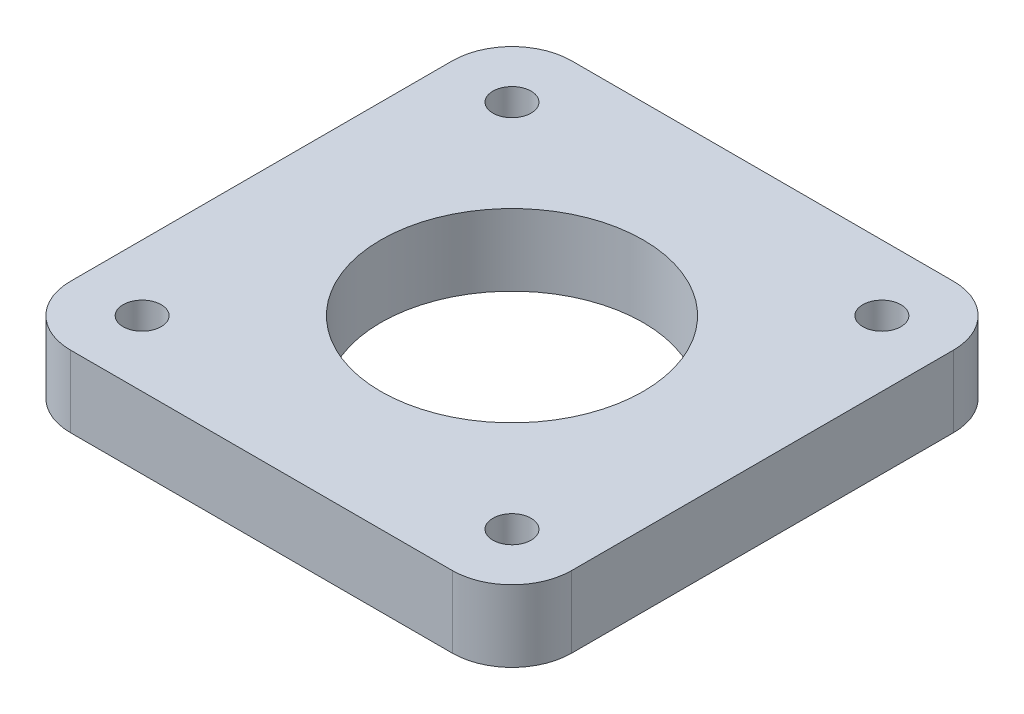
SolidWorks part; units mm, degrees
material "Maple"
ref_plane "Front Plane" through (0, 0, 0) normal (0, 0, 1) x (1, 0, 0)
ref_plane "Top Plane" through (0, 0, 0) normal (0, 1, 0) x (1, 0, 0)
ref_plane "Right Plane" through (0, 0, 0) normal (1, 0, 0) x (0, 0, -1)
sketch "Sketch1" plane through (0, 0, 0) normal (0, 1, 0) x (1, 0, 0)
  line L1 (-21, 21) -> (21, 21)
  line L2 (-21, 21) -> (-21, -21)
  line L3 (-21, -21) -> (21, -21)
  line L4 (21, 21) -> (21, -21)
  line L5 (-21, 21) -> (21, -21) construction
  line L6 (-21, -21) -> (21, 21) construction
  point P0 (0, 0)
  dimension "D1" = 42
extrude "Boss-Extrude1" add sketch "Sketch1" along normal blind 6
ref_plane "Plane1" through (0, 3, 0) normal (0, 1, 0) x (1, 0, 0)
hole_wizard "M3 Clearance Hole1" positions "Sketch5" profile "Sketch4" hole size "M3" standard "ANSI Metric" end condition through all
sketch "Sketch5" plane through (0, 0, 0) normal (0, -1, 0) x (0, 0, -1)
  circle A0 centre (-15.5, -15.5) radius 1.5 construction
  circle A1 centre (-15.5, 15.5) radius 1.5 construction
  circle A2 centre (15.5, 15.5) radius 1.5 construction
  circle A3 centre (15.5, -15.5) radius 1.5 construction
  point P0 (15.5, -15.5)
  point P2 (-15.5, -15.5)
  point P4 (-15.5, 15.5)
  point P6 (15.5, 15.5)
sketch "Sketch4" plane through (-15.5, 0, -15.5) normal (1, 0, 0) x (0, 0, -1)
  line L0 (0, 0) -> (0, 6)
  line L1 (0, 6) -> (1.6, 6)
  line L2 (1.6, 6) -> (1.6, 0)
  line L5 (1.6, 0) -> (0, 0)
  line L11 (0, -6.35) -> (0, 107.95) construction
  dimension "Thru Hole Dia." = 3.2
  dimension "Thru Hole Depth" = 6
sketch "Sketch6" plane through (0, 0, 0) normal (0, -1, 0) x (0, 0, 1)
  circle A0 centre (0, 0) radius 11
  circle A1 centre (0, 0) radius 11 construction
extrude "Cut-Extrude3" cut sketch "Sketch6" against normal through all
other "Smart-Feature1<x_nema 17-7>"
fillet "Fillet1" radius 5 4 edges at (21, 3, 21) (-21, 3, -21) (21, 3, -21) (-21, 3, 21)
